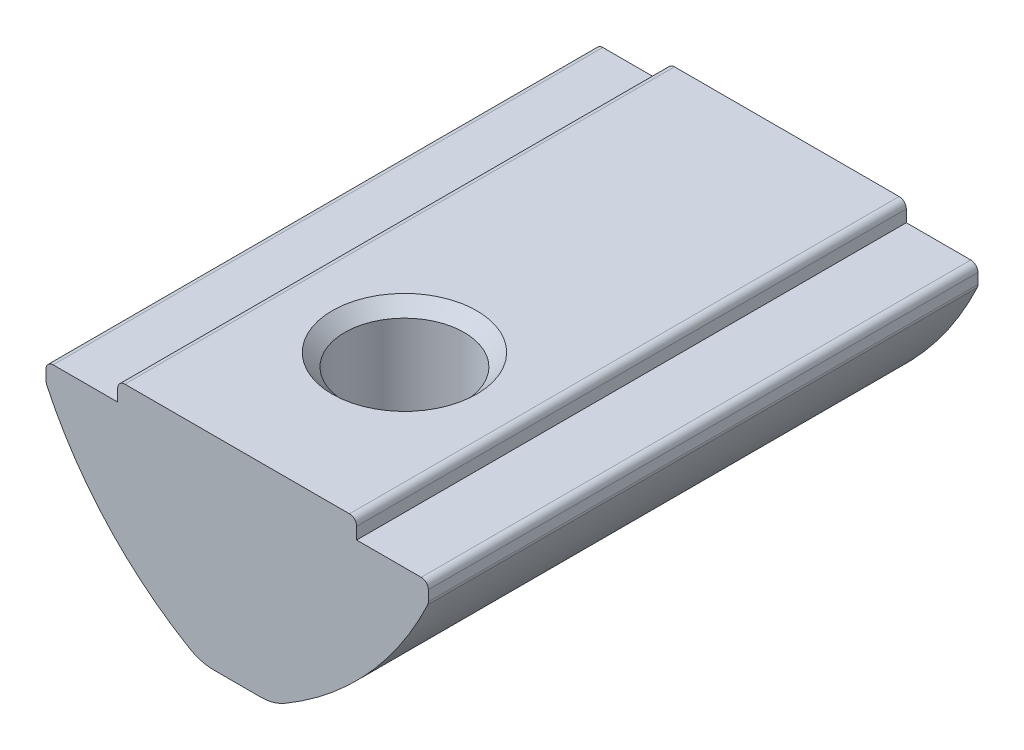
SolidWorks part; units mm, degrees
ref_plane "Спереди" through (0, 0, 0) normal (0, 0, 1) x (1, 0, 0)
ref_plane "Сверху" through (0, 0, 0) normal (0, 1, 0) x (1, 0, 0)
ref_plane "Справа" through (0, 0, 0) normal (1, 0, 0) x (0, 0, -1)
sketch "Эскиз1" plane through (0, 0, 0) normal (0, 0, 1) x (1, 0, 0)
  line L0 (-5, 0) -> (5, 0)
  line L5 (-5, 0) -> (-5, -0.8)
  line L6 (-5, -0.8) -> (-8, -0.8)
  line L7 (-8, -0.8) -> (-8, -1.6)
  line L8 (5, 0) -> (5, -0.8)
  line L9 (5, -0.8) -> (8, -0.8)
  line L10 (8, -0.8) -> (8, -1.6)
  line L11 (-1.5, -8.5) -> (1.5, -8.5)
  arc A0 (-8, -1.6) -> (-1.5, -8.5) centre (5.609, 4.7084) ccw
  arc A1 (1.5, -8.5) -> (8, -1.6) centre (-5.609, 4.7084) ccw
  point P0 (0, -8.5)
  point P4 (0, 0)
  dimension "D7" = 15
  dimension "D1" = 10
  dimension "D2" = 16
  dimension "D3" = 0.8
  dimension "D4" = 3
  dimension "D5" = 0.8
  dimension "D6" = 8.5
extrude "Бобышка-Вытянуть1" add sketch "Эскиз1" along normal mid plane 23
fillet "Скругление1" radius 0.3 6 edges at (8, -1.6, 0) (8, -0.8, 0) (-8, -0.8, 0) (-8, -1.6, 0) (5, 0, 0) (-5, 0, 0)
fillet "Скругление2" radius 2 2 edges at (1.5, -8.5, 0) (-1.5, -8.5, 0)
hole_wizard "Отверстие обработанное метчиком M63" positions "Эскиз2" profile "Эскиз4" tap size "M6" standard "ISO" end condition through all
sketch "Эскиз2" plane through (0, 0, 0) normal (0, 1, 0) x (1, 0, 0)
  line L0 (4.7, -11.5) -> (-4.7, -11.5) construction
  point P0 (0, -4.5)
  dimension "D1" = 7
sketch "Эскиз4" plane through (0, 0, 4.5) normal (1, 0, 0) x (0, 0, 1)
  line L0 (0, 0) -> (0, 8.5)
  line L1 (0, 8.5) -> (2.5, 8.5)
  line L2 (2.5, 8.5) -> (2.5, 0.525)
  line L3 (2.5, 0.525) -> (3.025, 0)
  line L5 (3.025, 0) -> (0, 0)
  line L6 (-2.5, 0.525) -> (-3.025, 0) construction
  line L11 (0, -6.35) -> (0, 107.95) construction
  dimension "Диаметр проходного сверла" = 5
  dimension "Глубина проходного сверла" = 8.5
  dimension "Диаметр передней зенковки" = 6.05
  dimension "Угол передней зенковки" = 90
cosmetic thread "Отверстие резьбы1" parameters "D2"=6
sketch "Эскиз5" plane through (0, 0, 0) normal (1, 0, 0) x (0, 0, -1)
  line L1 (6.5, -4.3) -> (6.5, -9.3) construction
  line L2 (11.5, -8.2244) -> (11.5, -1.6609) construction
  line L3 (6.5, -4.3) -> (6.5, -9.3)
  line L5 (11.5, -8.5) -> (-2.1987, -8.5) construction
  arc A0 (6.5, -4.3) -> (6.5, -9.3) centre (6.5, -6.8) ccw
  point P3 (4, -7.4722)
  dimension "D3" = 2.5
  dimension "D1" = 0.8
  dimension "D2" = 5
revolve "Повернуть1" add sketch "Эскиз5" angle 360 about L1
